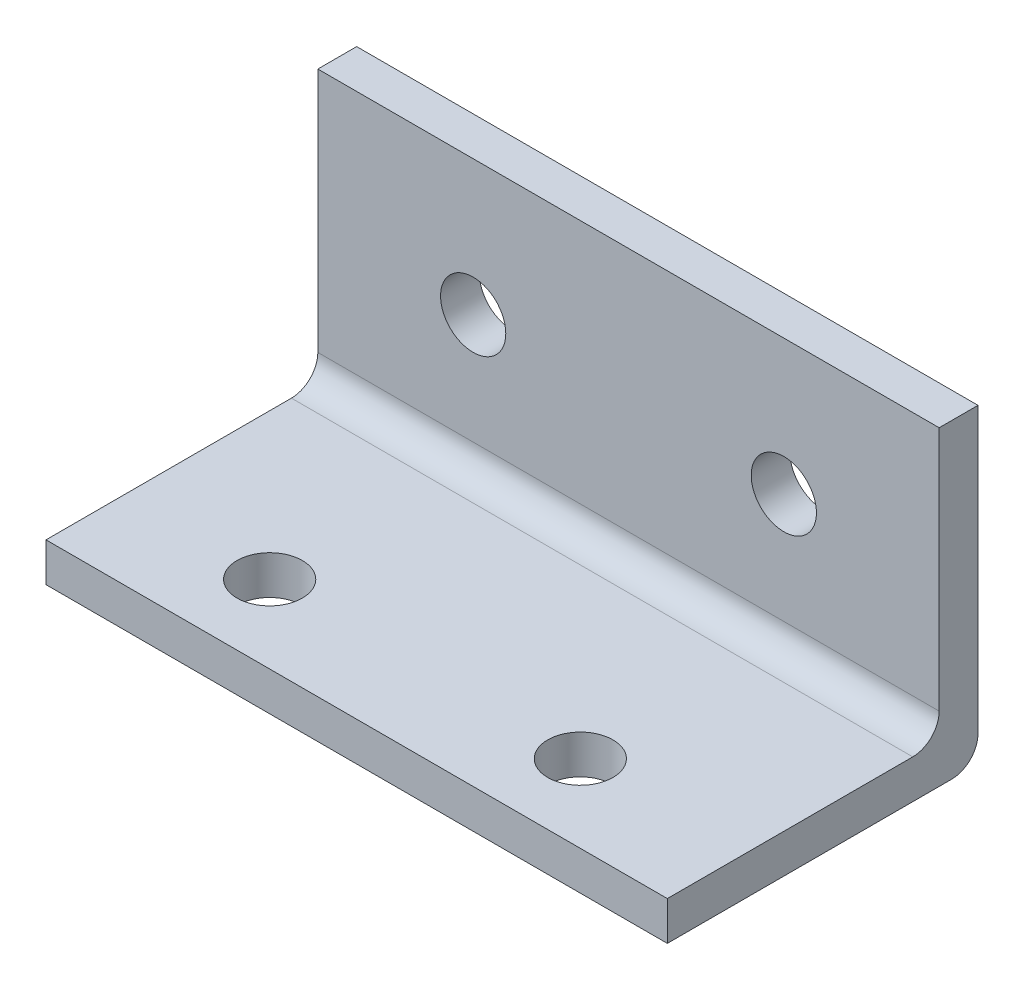
SolidWorks part; units mm, degrees
ref_plane "Front Plane" through (0, 0, 0) normal (0, 0, 1) x (1, 0, 0)
ref_plane "Top Plane" through (0, 0, 0) normal (0, 1, 0) x (1, 0, 0)
ref_plane "Right Plane" through (0, 0, 0) normal (1, 0, 0) x (0, 0, -1)
sketch "Sketch1" plane through (0, 0, 0) normal (1, 0, 0) x (0, 0, -1)
  line L0 (0, 0) -> (0, 25.4)
  line L1 (0, 0) -> (-25.4, 0)
  line L2 (-25.4, 0) -> (-25.4, 3.175)
  line L3 (-25.4, 3.175) -> (-3.175, 3.175)
  line L4 (-3.175, 3.175) -> (-3.175, 25.4)
  line L5 (-3.175, 25.4) -> (0, 25.4)
extrude "Boss-Extrude1" add sketch "Sketch1" along normal blind 50.8
sketch "Sketch2" plane through (0, 3.175, 0) normal (0, 1, 0) x (1, 0, 0)
  line L0 (0, 0) -> (0, -19.05)
  line L1 (0, -3.175) -> (0, -25.4) construction
  line L2 (0, -19.05) -> (11.938, -19.05)
  circle A0 centre (11.938, -19.05) radius 2.667
  circle A1 centre (37.338, -19.05) radius 2.667
  dimension "D1" = 2
extrude "Cut-Extrude1" cut sketch "Sketch2" against normal up to surface (3.175 mm away) up to face at (25.4, 0, 12.7)
sketch "Sketch3" plane through (0, 0, 3.175) normal (0, 0, 1) x (1, 0, 0)
  line L0 (50.8, 0) -> (50.8, 14.351)
  line L1 (50.8, 25.4) -> (50.8, 3.175) construction
  line L2 (50.8, 14.351) -> (38.1, 14.351)
  circle A0 centre (38.1, 14.351) radius 2.667
  circle A1 centre (12.7, 14.351) radius 2.667
  dimension "D1" = 2
extrude "Cut-Extrude2" cut sketch "Sketch3" against normal up to surface (3.175 mm away) up to face at (25.4, 12.7, 0)
fillet "Fillet1" radius 2.159 2 edges at (25.4, 0, 0) (25.4, 3.175, 3.175)
